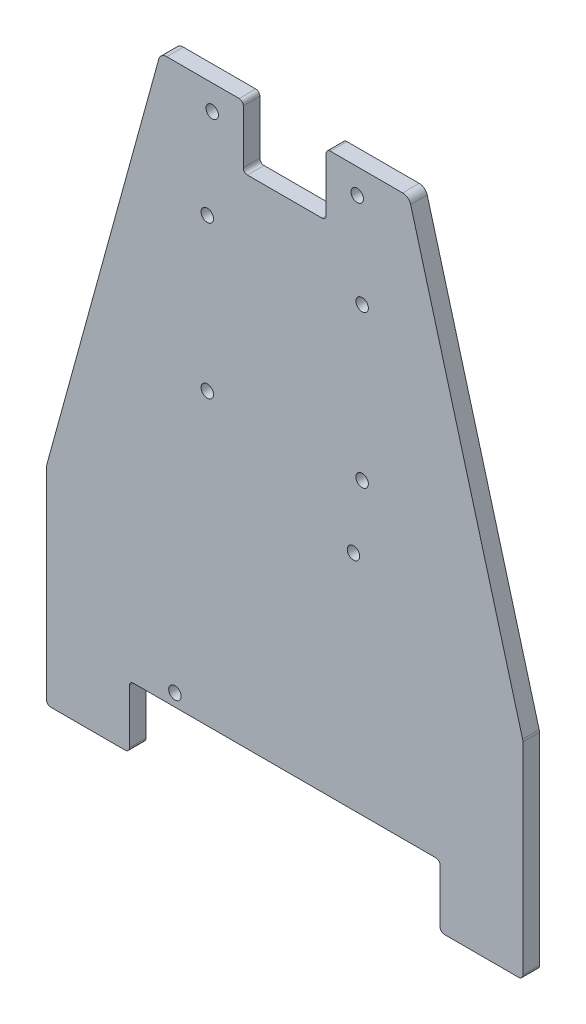
SolidWorks part; units mm, degrees
ref_plane "Front Plane" through (0, 0, 0) normal (0, 0, 1) x (1, 0, 0)
ref_plane "Top Plane" through (0, 0, 0) normal (0, 1, 0) x (1, 0, 0)
ref_plane "Right Plane" through (0, 0, 0) normal (1, 0, 0) x (0, 0, -1)
sketch "Sketch6" plane through (0, 0, 0) normal (0, 0, 1) x (1, 0, 0)
  line L1 (0, 0) -> (-115, 0)
  line L2 (0, 0) -> (0, 150)
  line L3 (0, 150) -> (-115, 150)
  line L4 (-115, 0) -> (-115, 150)
  dimension "D1" = 115
  dimension "D2" = 150
extrude "Boss-Extrude2" add sketch "Sketch6" along normal blind 4
sketch "Sketch7" plane through (0, 0, 4) normal (0, 0, 1) x (1, 0, 0)
  line L0 (-115, 0) -> (0, 0) construction
  line L1 (-95, 0) -> (-20, 0)
  line L2 (-95, 0) -> (-95, 15)
  line L3 (-95, 15) -> (-20, 15)
  line L4 (-20, 0) -> (-20, 15)
  line L5 (-115, 150) -> (-115, 0) construction
  line L6 (0, 0) -> (0, 150) construction
  dimension "D1" = 20
  dimension "D2" = 20
  dimension "D3" = 15
extrude "Cut-Extrude1" cut sketch "Sketch7" against normal through all
fillet "Fillet1" radius 1 6 edges at (-115, 0, 2) (0, 0, 2) (-20, 0, 2) (-95, 0, 2) (-95, 15, 2) (-20, 15, 2)
sketch "Sketch8" plane through (0, 0, 4) normal (0, 0, 1) x (1, 0, 0)
  line L0 (-57.5, 156.5622) -> (-57.5, -2.2369)
  line L1 (0, 150) -> (-115, 150) construction
  line L2 (-67.5, 150) -> (-47.5, 150)
  line L3 (-67.5, 150) -> (-67.5, 135)
  line L4 (-67.5, 135) -> (-47.5, 135)
  line L5 (-47.5, 150) -> (-47.5, 135)
  line L6 (0, 1) -> (0, 150) construction
  line L7 (-115, 150) -> (-115, 1) construction
  line M18 (0, 150) -> (-115, 150)
  dimension "D1" = 20
  dimension "D2" = 47.5
  dimension "D3" = 47.5
  dimension "D4" = 15
extrude "Cut-Extrude2" cut sketch "Sketch8" against normal through all contours L3 L4 L0 M18 | L5 L0 L4 M18
fillet "Fillet2" radius 1 4 edges at (-47.5, 135, 2) (-47.5, 150, 2) (-67.5, 150, 2) (-67.5, 135, 2)
sketch "Sketch11" plane through (0, 0, 4) normal (0, 0, 1) x (1, 0, 0)
  line L0 (-87.5, 150) -> (-115, 50)
  line L1 (-68.5, 150) -> (-115, 150) construction
  line L2 (-115, 150) -> (-115, 1) construction
  line L3 (-115, 50) -> (-115, 150)
  line L4 (-115, 150) -> (-87.5, 150)
  line L5 (-67.5, 149) -> (-67.5, 136) construction
  line L6 (-114, 0) -> (-96, 0) construction
  line L7 (-66.5, 135) -> (-48.5, 135) construction
  line L9 (-57.5, 135) -> (-57.5, 15)
  line L10 (-21, 15) -> (-94, 15) construction
  line L11 (0, 50) -> (0, 150)
  line L12 (-27.5, 150) -> (0, 50)
  line L13 (0, 150) -> (-27.5, 150)
  point P12 (-105, 0)
  dimension "D1" = 20
  dimension "D2" = 50
extrude "Cut-Extrude3" cut sketch "Sketch11" against normal through all contours L11 L13 L12 | L3 L4 L0
fillet "Fillet3" radius 2 4 edges at (-115, 50, 2) (-87.5, 150, 2) (-27.5, 150, 2) (0, 50, 2)
sketch "Sketch14" plane through (0, 0, 0) normal (0, 0, -1) x (-1, 0, 0)
  line L0 (66.5, 135) -> (48.5, 135) construction
  line L2 (68.5, 150) -> (85.9758, 150) construction
  line L3 (29.0242, 150) -> (46.5, 150) construction
  circle A0 centre (40, 144) radius 1.5
  circle A1 centre (75, 144) radius 1.5
  point P2 (57.5, 135)
  point P12 (37.7621, 150)
  dimension "D1" = 17.5
  dimension "D3" = 3
  dimension "D4" = 3
  dimension "D2" = 17.5
  dimension "D5" = 6
  dimension "D6" = 6
extrude "Cut-Extrude4" cut sketch "Sketch14" against normal through all
sketch "Sketch17" plane through (0, 0, 4) normal (0, 0, 1) x (1, 0, 0)
  line L0 (-19, 0) -> (-1, 0) construction
  line L1 (0, 1) -> (0, 49.73) construction
  line L2 (-115, 49.73) -> (-115, 1) construction
  circle A0 centre (-76.19, 121.74) radius 1.5
  circle A1 centre (-38.81, 121.74) radius 1.5
  circle A2 centre (-76.19, 85) radius 1.5
  circle A3 centre (-38.81, 85) radius 1.5
  dimension "D1" = 3
  dimension "D2" = 3
  dimension "D3" = 3
  dimension "D4" = 3
  dimension "D5" = 36.74
  dimension "D6" = 36.74
  dimension "D7" = 37.38
  dimension "D8" = 37.38
  dimension "D9" = 85
  dimension "D10" = 38.81
  dimension "D11" = 38.81
  dimension "D12" = 121.74
extrude "Cut-Extrude6" cut sketch "Sketch17" against normal through all
sketch "Sketch18" plane through (0, 0, 4) normal (0, 0, 1) x (1, 0, 0)
  line L1 (-115, 49.73) -> (-115, 1) construction
  line L2 (-21, 15) -> (-94, 15) construction
  circle A0 centre (-84, 18) radius 1.5
  circle A1 centre (-40.9, 68.8) radius 1.5
  point P6 (-80.3399, 12.5103)
  point P9 (-83.4255, 19.3569)
  dimension "D1" = 3
  dimension "D2" = 3
  dimension "D3" = 43.1
  dimension "D4" = 50.8
  dimension "D5" = 31
  dimension "D6" = 3
extrude "Cut-Extrude7" cut sketch "Sketch18" against normal through all
